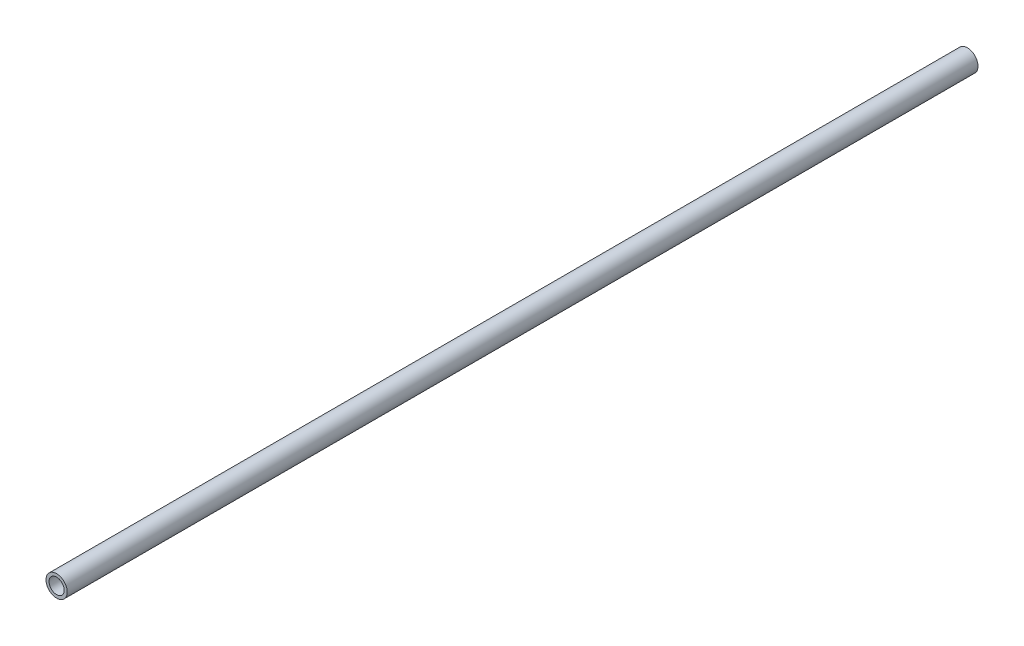
SolidWorks part; units mm, degrees
ref_plane "Front Plane" through (0, 0, 0) normal (0, 0, 1) x (1, 0, 0)
ref_plane "Top Plane" through (0, 0, 0) normal (0, 1, 0) x (1, 0, 0)
ref_plane "Right Plane" through (0, 0, 0) normal (1, 0, 0) x (0, 0, -1)
sketch "Sketch1" plane through (0, 0, 0) normal (0, 0, 1) x (1, 0, 0)
  circle A0 centre (47.9171, 71.5483) radius 3.5
  circle A1 centre (47.9171, 71.5483) radius 2.5
  dimension "D1" = 1
extrude "Boss-Extrude1" add sketch "Sketch1" against normal mid plane 300
